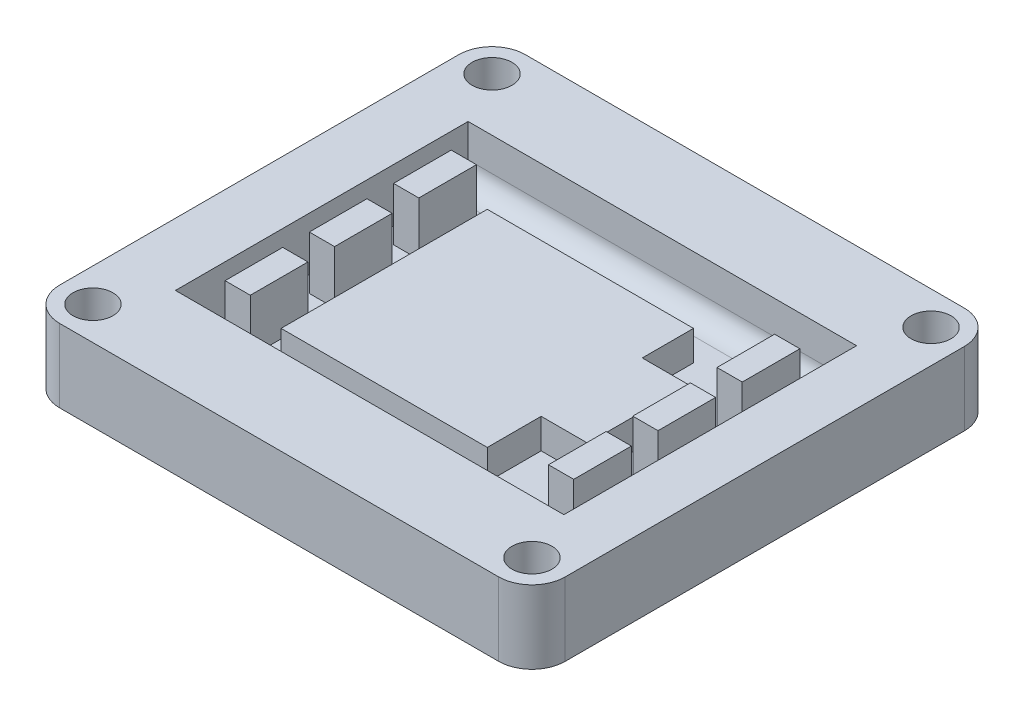
SolidWorks part; units mm, degrees
ref_plane "Front" through (0, 0, 0) normal (0, 0, 1) x (1, 0, 0)
ref_plane "Top" through (0, 0, 0) normal (0, 1, 0) x (1, 0, 0)
ref_plane "Right" through (0, 0, 0) normal (1, 0, 0) x (0, 0, -1)
sketch "Sketch2" plane through (0, 0, 0) normal (0, 1, 0) x (1, 0, 0)
  line L0 (-33, 35) -> (-33, -35) construction
  line L1 (-33, -35) -> (33, -35)
  line L2 (-38, -30) -> (-38, 30)
  line L3 (-33, 35) -> (33, 35)
  line L4 (38, -30) -> (38, 30)
  line L5 (-38, -35) -> (38, 35) construction
  line L6 (-38, 35) -> (38, -35) construction
  line L7 (-38, -30) -> (38, -30) construction
  line L8 (33, -35) -> (33, 35) construction
  line L9 (38, 30) -> (-38, 30) construction
  arc A0 (-33, -35) -> (-38, -30) centre (-33, -30) cw
  arc A1 (33, -35) -> (38, -30) centre (33, -30) ccw
  arc A2 (33, 35) -> (38, 30) centre (33, 30) cw
  arc A3 (-38, 30) -> (-33, 35) centre (-33, 30) cw
  circle A4 centre (-33, 30) radius 3
  circle A5 centre (-33, -30) radius 3
  circle A6 centre (33, 30) radius 3
  circle A7 centre (33, -30) radius 3
  point P0 (0, 0)
  point P22 (105, 35)
  dimension "D3" = 5
  dimension "D1" = 76
  dimension "D2" = 70
extrude "Boss-Extrude1" add sketch "Sketch2" along normal blind 25
sketch "Sketch5" plane through (0, 25, 0) normal (0, 1, 0) x (1, 0, 0)
  line L1 (-100, 22) -> (100, 22)
  line L2 (-100, 22) -> (-100, -22)
  line L3 (-100, -22) -> (100, -22)
  line L4 (100, 22) -> (100, -22)
  line L5 (-100, 22) -> (100, -22) construction
  line L6 (-100, -22) -> (100, 22) construction
  point P0 (0, 0)
  dimension "D1" = 200
  dimension "D2" = 44
extrude "Cut-Extrude1" cut sketch "Sketch5" against normal blind 8
sketch "Sketch6" plane through (87.6229, 17, 0) normal (0, 1, 0) x (1, 0, 0)
  line L1 (-106.8395, 15.5) -> (-75.8395, 15.5)
  line L2 (-106.8395, 15.5) -> (-106.8395, -15.5)
  line L3 (-106.8395, -15.5) -> (-75.8395, -15.5)
  line L5 (-106.8395, 15.5) -> (-75.8395, -15.5) construction
  line L6 (-106.8395, -15.5) -> (-75.8395, 15.5) construction
  line L7 (-75.8395, 15.5) -> (-75.8395, 7.8)
  line L8 (-75.8395, -7.4) -> (-68.8395, -7.4)
  line L10 (-75.8395, 7.8) -> (-68.8395, 7.8)
  line L11 (-68.8395, -7.4) -> (-68.8395, 7.8)
  line L12 (-75.8395, -7.4) -> (-75.8395, -15.5)
  point P0 (-91.3395, 0)
  dimension "D1" = 31
  dimension "D2" = 31
  dimension "D3" = 8.1
  dimension "D4" = 7.7
  dimension "D5" = 7
extrude "SensorModule(bottomMiddlee)" add sketch "Sketch6" along normal blind 4.5
sketch "Sketch12" plane through (0, 0, 0) normal (0, -1, 0) x (1, 0, 0)
  line L1 (-124.8645, 44.848) -> (123.0106, 44.848)
  line L2 (-124.8645, 44.848) -> (-124.8645, -57.584)
  line L3 (-124.8645, -57.584) -> (123.0106, -57.584)
  line L4 (123.0106, 44.848) -> (123.0106, -57.584)
extrude "Cut-Extrude2" cut sketch "Sketch12" against normal blind 14
sketch "Sketch14" plane through (0, 0, -22) normal (0, 0, 1) x (1, 0, 0)
  line L0 (38, 25) -> (-38, 25) construction
  line L1 (-38, 17) -> (-28.5979, 17)
  line L2 (-38, 17) -> (-38, 25)
  line L3 (-38, 25) -> (-28.5979, 25)
  line L4 (-28.5979, 17) -> (-28.5979, 25)
  line L6 (29.8005, 25) -> (38, 25)
  line L7 (29.8005, 25) -> (29.8005, 17)
  line L8 (29.8005, 17) -> (38, 17)
  line L9 (38, 25) -> (38, 17)
  point P12 (0, 0)
  point P13 (0, 0)
  point P14 (-31.6803, 25)
  point P15 (31.9442, 25)
  point P16 (-30.2996, 25)
  point P17 (-28.5979, 25)
  point P18 (29.8005, 25)
extrude "Boss-Extrude2" add sketch "Sketch14" along normal blind 48
fillet "Fillet1" radius 3 1 edges at (0.6013, 17, -22)
fillet "Fillet2" radius 3 1 edges at (0.6013, 17, 22)
sketch "Sketch15" plane through (3.4894, 17, 0) normal (0, 1, 0) x (1, 0, 0)
  line L1 (-29.6262, 17) -> (-25.8326, 17)
  line L2 (-29.6262, 17) -> (-29.6262, 8.3333)
  line L3 (-29.6262, 8.3333) -> (-25.8326, 8.3333)
  line L4 (-25.8326, 17) -> (-25.8326, 8.3333)
  line L5 (-29.6262, -4.3333) -> (-25.8326, -4.3333)
  line L6 (-29.6262, -4.3333) -> (-29.6262, 4.3333)
  line L7 (-29.6262, 4.3333) -> (-25.8326, 4.3333)
  line L8 (-25.8326, -4.3333) -> (-25.8326, 4.3333)
  line L9 (-29.6262, -8.3333) -> (-25.8326, -8.3333)
  line L10 (-29.6262, -8.3333) -> (-29.6262, -17)
  line L11 (-29.6262, -17) -> (-25.8326, -17)
  line L12 (-25.8326, -8.3333) -> (-25.8326, -17)
  point P12 (0, 0)
  point P13 (0, 0)
  point P14 (-27.7294, -4.3333)
  point P15 (-29.1725, 12.9334)
  point P16 (-29.6262, 5.0441)
  point P17 (-25.8326, -4.8568)
  dimension "D1" = 4
  dimension "D2" = 4
extrude "Boss-Extrude3" add sketch "Sketch15" along normal blind 8
sketch "Sketch16" plane through (51.9461, 25, 9.7102) normal (0, 1, 0) x (1, 0, 0)
  line L1 (-29.8032, 27.0559) -> (-26.0096, 27.0559)
  line L2 (-29.8032, 27.0559) -> (-29.8032, 18.3892)
  line L3 (-29.8032, 18.3892) -> (-26.0096, 18.3892)
  line L4 (-26.0096, 27.0559) -> (-26.0096, 18.3892)
  line L5 (-29.8032, 5.7226) -> (-26.0096, 5.7226)
  line L6 (-29.8032, 5.7226) -> (-29.8032, 14.3892)
  line L7 (-29.8032, 14.3892) -> (-26.0096, 14.3892)
  line L8 (-26.0096, 5.7226) -> (-26.0096, 14.3892)
  line L9 (-29.8032, 1.7226) -> (-26.0096, 1.7226)
  line L10 (-29.8032, 1.7226) -> (-29.8032, -6.9441)
  line L11 (-29.8032, -6.9441) -> (-26.0096, -6.9441)
  line L12 (-26.0096, 1.7226) -> (-26.0096, -6.9441)
  point P12 (-0.177, 10.0559)
  point P13 (-0.177, 10.0559)
  point P14 (-27.9064, 5.7226)
  point P15 (-29.3495, 22.9893)
  point P16 (-29.8032, 15.1)
  point P17 (-26.0096, 5.1991)
  dimension "D1" = 4
  dimension "D2" = 4
extrude "Boss-Extrude4" add sketch "Sketch16" against normal blind 10
